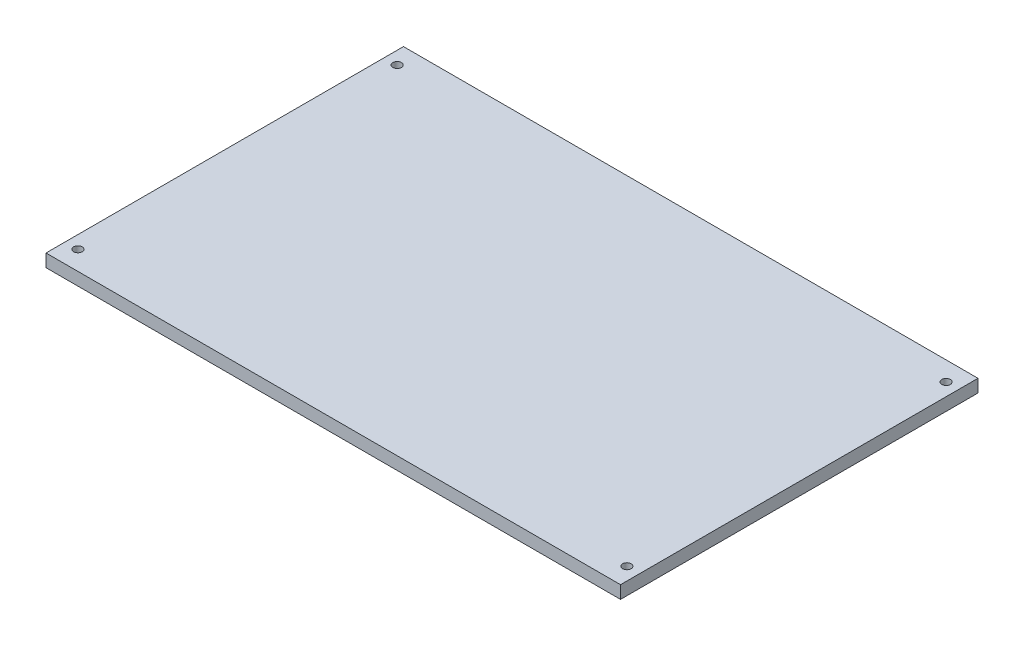
SolidWorks part; units mm, degrees
material "Copper"
ref_plane "Front Plane" through (0, 0, 0) normal (0, 0, 1) x (1, 0, 0)
ref_plane "Top Plane" through (0, 0, 0) normal (0, 1, 0) x (1, 0, 0)
ref_plane "Right Plane" through (0, 0, 0) normal (1, 0, 0) x (0, 0, -1)
sketch "Sketch1" plane through (0, 0, 0) normal (0, 1, 0) x (1, 0, 0)
  line L1 (-20, -52.1122) -> (880, -52.1122)
  line L2 (-20, -52.1122) -> (-20, 507.8878)
  line L3 (-20, 507.8878) -> (880, 507.8878)
  line L4 (880, -52.1122) -> (880, 507.8878)
extrude "Boss-Extrude1" add sketch "Sketch1" along normal blind 20
ref_plane "Plane1" through (0, 0, 0) normal (0, -1, 0) x (-1, 0, 0)
sketch "Sketch2" plane through (0, 0, 0) normal (0, -1, 0) x (-1, 0, 0)
  line L1 (-880, 507.8878) -> (20, 507.8878)
  line L2 (-880, 507.8878) -> (-880, -52.1122)
  line L3 (-880, -52.1122) -> (20, -52.1122)
  line L4 (20, 507.8878) -> (20, -52.1122)
  point P7 (-860, 477.8878)
  point P11 (0, 477.8878)
  point P12 (0, -22.1122)
  point P13 (-860, -22.1122)
  dimension "D1" = 20
  dimension "D2" = 20
  dimension "D3" = 20
  dimension "D4" = 20
  dimension "D5" = 30
  dimension "D6" = 30
  dimension "D7" = 30
  dimension "D8" = 30
hole_wizard "CBORE for 1/2 Heavy Hex Bolt1" positions "3DSketch1" profile "Sketch3" counterbore size "1/2" standard "ANSI Inch"
sketch3d "3DSketch1"
  point P0 (0, 0, -477.8878)
  point P3 (860, 0, -477.8878)
  point P6 (860, 0, 22.1122)
  point P9 (0, 0, 0)
  point P13 (0, 0, 22.1122)
sketch "Sketch3" plane through (0, 0, -477.8878) normal (1, 0, 0) x (0, 0, -1)
  line L0 (0, 0) -> (0, 20)
  line L1 (0, 20) -> (6.7462, 20)
  line L3 (6.7462, 20) -> (6.7462, 9.2456)
  line L4 (14.2875, 9.2456) -> (6.7462, 9.2456)
  line L5 (14.2875, 9.2456) -> (14.2875, 0.635)
  line L6 (14.2875, 0.635) -> (14.9225, 0)
  line L7 (14.9225, 0) -> (0, 0)
  line L8 (-14.2875, 0.635) -> (-14.9225, 0) construction
  line L11 (0, -6.35) -> (0, 107.95) construction
  dimension "Thru Hole Dia." = 13.4925
  dimension "Thru Hole Depth" = 20
  dimension "C'Bore Dia." = 28.575
  dimension "C'Bore Depth" = 9.2456
  dimension "Near C'Sink Dia." = 29.845
  dimension "Near C'Sink Angle" = 90
